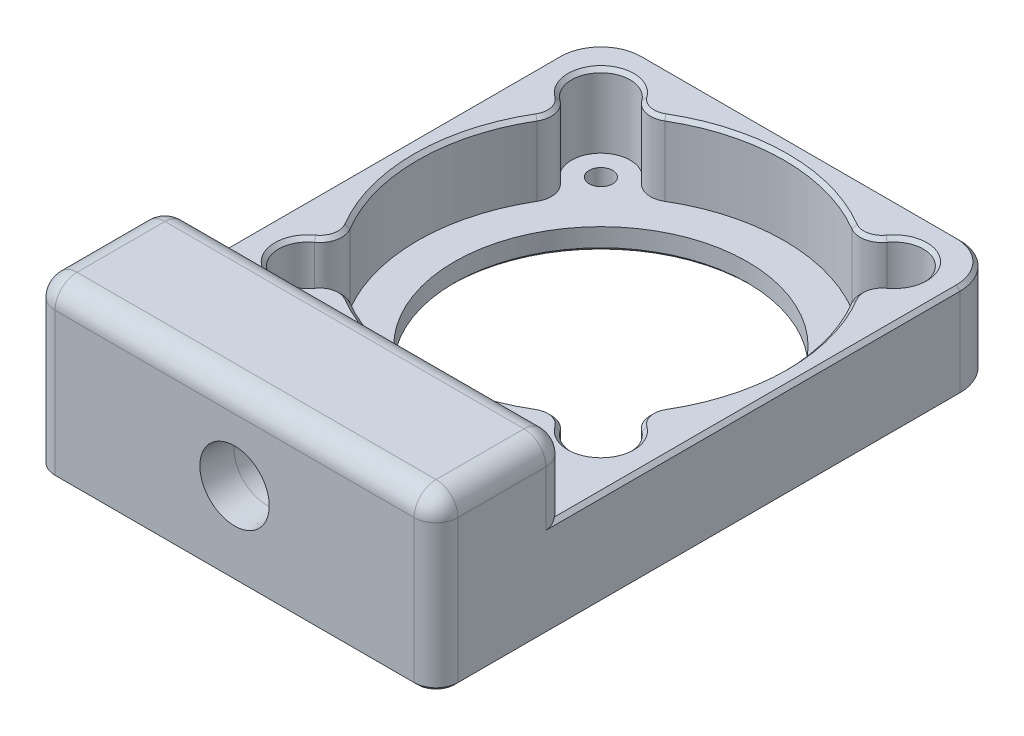
SolidWorks part; units mm, degrees
ref_plane "Front Plane" through (0, 0, 0) normal (0, 0, 1) x (1, 0, 0)
ref_plane "Top Plane" through (0, 0, 0) normal (0, 1, 0) x (1, 0, 0)
ref_plane "Right Plane" through (0, 0, 0) normal (1, 0, 0) x (0, 0, -1)
sketch "MountingPattern" plane through (0, 0, 0) normal (0, 1, 0) x (1, 0, 0)
  line L1 (-20, -20) -> (20, -20) construction
  line L2 (-20, -20) -> (-20, 20) construction
  line L3 (-20, 20) -> (20, 20) construction
  line L4 (20, -20) -> (20, 20) construction
  line L5 (-20, -20) -> (20, 20) construction
  line L6 (-20, 20) -> (20, -20) construction
  circle A0 centre (-20, 20) radius 1.75
  circle A1 centre (20, 20) radius 1.75
  circle A2 centre (20, -20) radius 1.75
  circle A3 centre (-20, -20) radius 1.75
  point P0 (0, 0)
  point P11 (0, 0)
  dimension "D1" = 3.5
  dimension "D2" = 40
sketch "CameraBody" plane through (0, 0, 0) normal (0, 1, 0) x (1, 0, 0)
  line L0 (-20, 20) -> (20, 20) construction
  line L1 (-23.75, 22.1844) -> (23.75, 22.1844) construction
  line L2 (-23.75, 22.1844) -> (-23.75, -47.818) construction
  line L3 (-23.75, -47.818) -> (23.75, -47.818) construction
  line L4 (23.75, 22.1844) -> (23.75, -47.818) construction
  point P0 (0, 22.1844)
  dimension "D1" = 47.5
  dimension "D2" = 70.0024
  dimension "D3" = 2.1844
sketch "Sketch3" plane through (0, 0, 0) normal (0, 1, 0) x (1, 0, 0)
  line L0 (27.5, 20) -> (20, 20) construction
  line L1 (-27.5, 27.5) -> (27.5, 27.5)
  line L2 (-27.5, 27.5) -> (-27.5, -50)
  line L3 (-27.5, -50) -> (27.5, -50)
  line L4 (27.5, 27.5) -> (27.5, -50)
  line L5 (20, 20) -> (20, 27.5) construction
  circle A0 centre (0, 0) radius 20
  circle A21 centre (-20, 20) radius 1.6
  circle A22 centre (20, 20) radius 1.6
  circle A23 centre (20, -20) radius 1.6
  circle A24 centre (-20, -20) radius 1.6
  point P7 (0, 27.5)
  dimension "D1" = 40
  dimension "D3" = 3.2
  dimension "D2" = 55
  dimension "D4" = 50
extrude "Boss-Extrude1" add sketch "Sketch3" along normal blind 3
sketch "Sketch4" plane through (0, 3, 0) normal (0, 1, 0) x (1, 0, 0)
  line L0 (27.5, 27.5) -> (-27.5, 27.5) construction
  line L1 (-27.5, -50) -> (27.5, -50) construction
  line L2 (27.5, -50) -> (27.5, 27.5) construction
  line L3 (-27.5, 27.5) -> (-27.5, -50) construction
  line L4 (-27.5, -50) -> (27.5, -50)
  line L5 (27.5, -50) -> (27.5, 27.5)
  line L6 (-27.5, 27.5) -> (-27.5, -50)
  line L7 (27.5, 27.5) -> (-27.5, 27.5)
  circle A0 centre (0, 0) radius 25
  dimension "D1" = 50
extrude "Boss-Extrude2" add sketch "Sketch4" along normal blind 10
sketch "Sketch5" plane through (0, 3, 0) normal (0, -1, 0) x (1, 0, 0)
  circle A0 centre (20, -20) radius 4
  circle A1 centre (-20, -20) radius 4
  circle A2 centre (-20, 20) radius 4
  circle A3 centre (20, 20) radius 4
  dimension "D1" = 8
extrude "Cut-Extrude1" cut sketch "Sketch5" against normal through all
fillet "Fillet1" radius 3 8 edges at (19.129, 8, -16.096) (16.096, 8, -19.129) (-19.129, 8, 16.096) (-16.096, 8, 19.129) (16.096, 8, 19.129) (19.129, 8, 16.096) (-16.096, 8, -19.129) (-19.129, 8, -16.096)
fillet "Fillet2" radius 6 2 edges at (27.5, 6.5, -27.5) (-27.5, 6.5, -27.5)
sketch "Sketch6" plane through (0, 13, 0) normal (0, 1, 0) x (1, 0, 0)
  line L0 (27.5, -50) -> (27.5, 21.5) construction
  line L1 (-27.5, -50) -> (27.5, -50)
  line L2 (-27.5, -50) -> (-27.5, -32)
  line L3 (-27.5, -32) -> (27.5, -32)
  line L4 (27.5, -50) -> (27.5, -32)
  dimension "D1" = 32
extrude "Boss-Extrude3" add sketch "Sketch6" along normal blind 10
sketch "Sketch7" plane through (0, 0, 50) normal (0, 0, 1) x (1, 0, 0)
  line L0 (-27.5, 23) -> (-27.5, 0) construction
  circle A0 centre (0, 11.5) radius 4.4323
  point P5 (-27.5, 11.5)
  dimension "D1" = 8.8646
extrude "TripodMount" cut sketch "Sketch7" against normal blind 12
fillet "Fillet3" radius 3 8 edges at (27.5, 11.5, 50) (-27.5, 11.5, 50) (27.5, 18, 32) (-27.5, 18, 32) (0, 23, 32) (27.5, 23, 41) (0, 23, 50) (-27.5, 23, 41)
chamfer "Chamfer1" distance 0.5 angle 45 13 edges at (-20, 0, -18.4) (-20, 0, 21.6) (20, 0, 21.6) (20, 0, -18.4) (0, 0, 20) (-25.7426, 0, -25.7426) (-27.5, 0, 12.75) (0, 0, 50) (27.5, 0, 12.75) (25.7426, 0, -25.7426) (0, 0, -27.5) (-26.6213, 0, 49.1213) (26.6213, 0, 49.1213)
chamfer "Chamfer3" distance 0.5 angle 45 21 edges at (27.5, 13, 6.75) (-27.5, 13, 6.75) (25.7426, 13, -25.7426) (-25.7426, 13, -25.7426) (0, 13, -27.5) (0, 13, 25) (14.9216, 13, 21.1342) (-14.9216, 13, 21.1342) (22.8284, 13, 22.8284) (-22.8284, 13, 22.8284) (21.1342, 13, 14.9216) (-21.1342, 13, 14.9216) (25, 13, 0) (-25, 13, 0) (21.1342, 13, -14.9216) (-21.1342, 13, -14.9216) (22.8284, 13, -22.8284) (-22.8284, 13, -22.8284) (14.9216, 13, -21.1342) (-14.9216, 13, -21.1342) (0, 13, -25)
chamfer "ChamferTripodMount" distance 0.3048 angle 86 1 edges at (4.4323, 11.5, 50)
